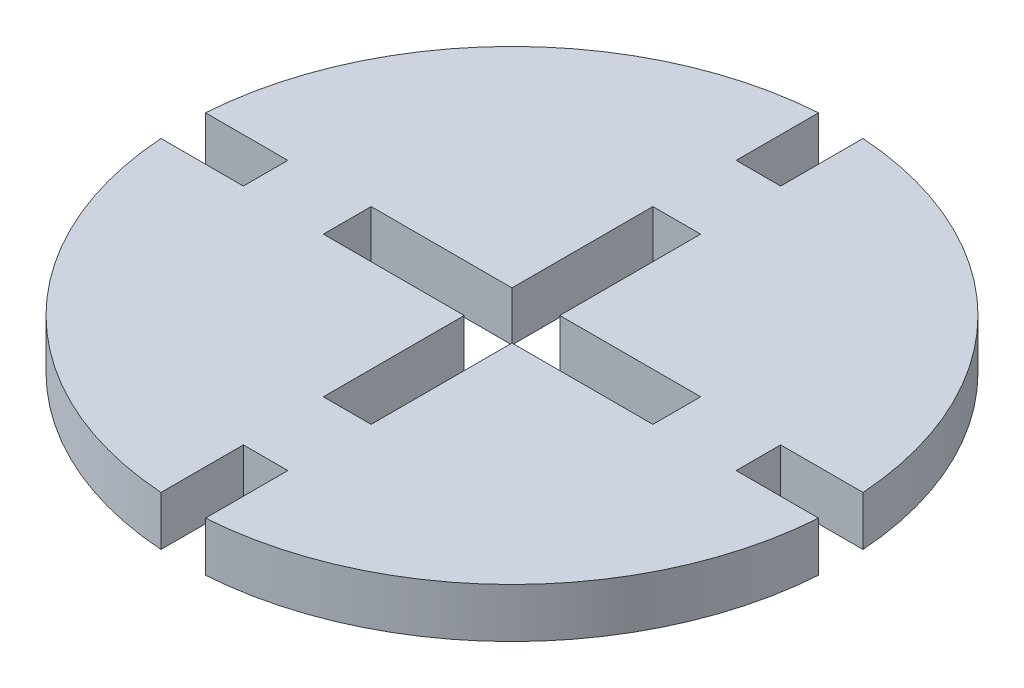
SolidWorks part; units mm, degrees
ref_plane "Alzado" through (0, 0, 0) normal (0, 0, 1) x (1, 0, 0)
ref_plane "Planta" through (0, 0, 0) normal (0, 1, 0) x (1, 0, 0)
ref_plane "Vista lateral" through (0, 0, 0) normal (1, 0, 0) x (0, 0, -1)
sketch "Sketch1" plane through (0, 0, 0) normal (0, 1, 0) x (1, 0, 0)
  line L0 (48.4783, 121.7343) -> (242.3913, 121.7343) construction
  line L22 (0, 18.8238) -> (0, -18.4966) construction
  line L34 (-16.3461, 0) -> (18.4218, 0) construction
  line L37 (1.35, 14.9544) -> (-1.35, 14.9544)
  line L38 (-1.35, 14.9544) -> (-1.35, 19.9544)
  line L39 (-19.9544, 1.35) -> (-14.9544, 1.35)
  line L40 (-14.9544, 1.35) -> (-14.9544, -1.35)
  line L43 (-19.9544, -1.35) -> (-14.9544, -1.35)
  line L44 (1.35, -14.9544) -> (-1.35, -14.9544)
  line L45 (-1.35, -14.9544) -> (-1.35, -19.9544)
  line L46 (1.35, -14.9544) -> (1.35, -19.9544)
  line L47 (19.9544, -1.35) -> (14.9544, -1.35)
  line L48 (14.9544, 1.35) -> (14.9544, -1.35)
  line L49 (19.9544, 1.35) -> (14.9544, 1.35)
  line L50 (1.35, 14.9544) -> (1.35, 19.9544)
  arc A7 (-1.35, 19.9544) -> (-19.9544, 1.35) centre (0, 0) ccw
  arc A8 (-1.35, -19.9544) -> (-19.9544, -1.35) centre (0, 0) cw
  arc A9 (1.35, -19.9544) -> (19.9544, -1.35) centre (0, 0) ccw
  arc A10 (1.35, 19.9544) -> (19.9544, 1.35) centre (0, 0) cw
  point P6 (-14.9544, 0)
  point P19 (0, -14.9544)
  point P26 (0, 14.9544)
extrude "Boss-Extrude1" add sketch "Sketch1" along normal blind 3
sketch "Sketch3" plane through (0, 3, 0) normal (0, 1, 0) x (1, 0, 0)
  line L0 (1.45, 1.45) -> (10, 1.45)
  line L1 (-10, -1.45) -> (-1.45, -1.45)
  line L2 (-10, -1.45) -> (-10, 1.45)
  line L3 (-10, 1.45) -> (-1.45, 1.45)
  line L4 (10, -1.45) -> (10, 1.45)
  line L5 (-10, -1.45) -> (10, 1.45) construction
  line L6 (-10, 1.45) -> (10, -1.45) construction
  line L7 (-1.45, -10) -> (1.45, -10)
  line L8 (-1.45, -10) -> (-1.45, -1.45)
  line L9 (-1.45, 10) -> (1.45, 10)
  line L10 (1.45, -10) -> (1.45, -1.45)
  line L11 (-1.45, -10) -> (1.45, 10) construction
  line L12 (-1.45, 10) -> (1.45, -10) construction
  line L13 (1.45, -1.45) -> (10, -1.45)
  line L14 (-1.45, 1.45) -> (-1.45, 10)
  line L15 (1.45, 1.45) -> (1.45, 10)
  point P0 (0, 0)
  point P5 (0, 0)
extrude "Cut-Extrude1" cut sketch "Sketch3" against normal up to next
equation "\"material\"= 3"
equation "\"kerf\"= \"material\" - 0.3mm"
equation "\"large\"= 90"
equation "\"Radius\"= 10"
equation "\"D2@Sketch3\"=\"subkerf\""
equation "\"D4@Sketch1\"=\"kerf\"/2"
equation "\"D5@Sketch1\"=\"kerf\"/2"
equation "\"D4@Sketch3\"=\"subkerf\""
equation "\"D1@Boss-Extrude1\"=\"material\""
equation "\"subkerf\"= \"material\" - 0.1mm"
